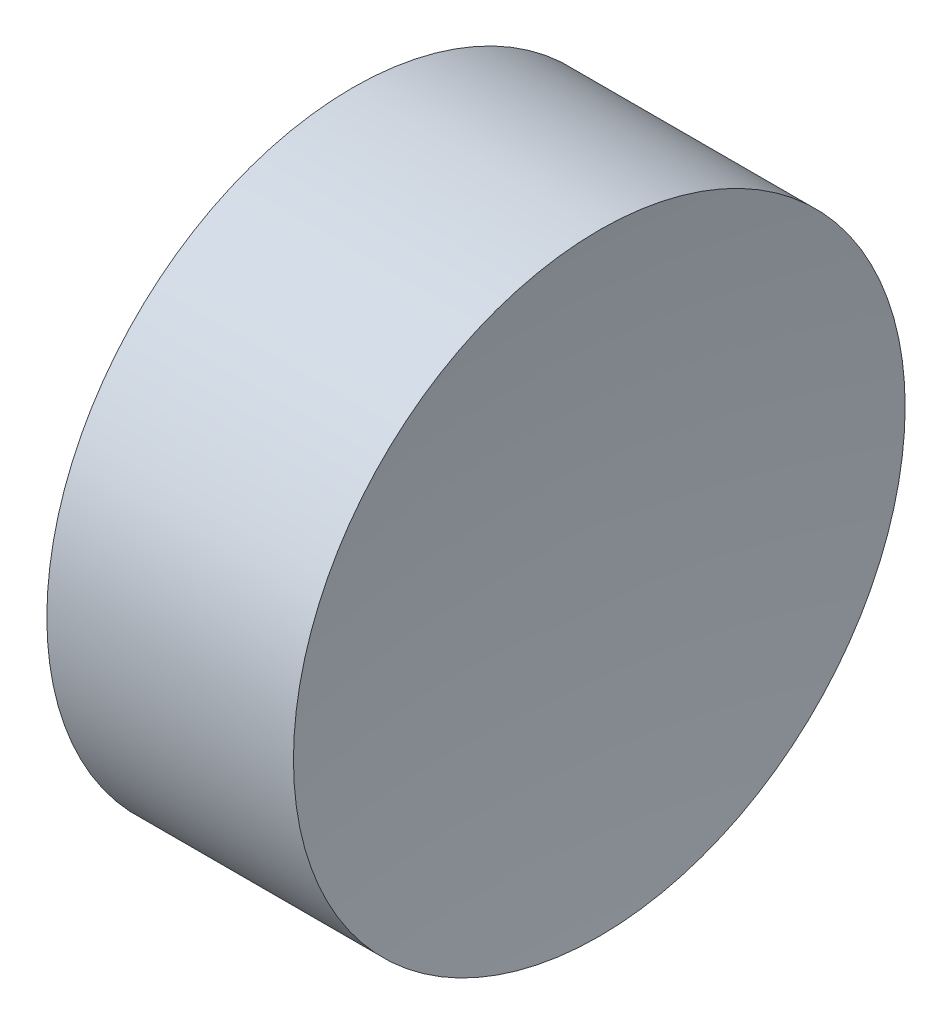
SolidWorks part; units mm, degrees
ref_plane "前视基准面" through (0, 0, 0) normal (0, 0, 1) x (1, 0, 0)
ref_plane "上视基准面" through (0, 0, 0) normal (0, 1, 0) x (1, 0, 0)
ref_plane "右视基准面" through (0, 0, 0) normal (1, 0, 0) x (0, 0, -1)
sketch "草图1" plane through (0, 0, 0) normal (0, 0, 1) x (1, 0, 0)
  line L0 (10.6125, 6.5223) -> (13.9161, 6.5223) construction
  line L1 (12.5141, 6.5223) -> (11.5141, 6.5223)
  line L3 (12.0141, 8.0223) -> (12.6159, 8.0223)
  line L4 (12.0141, 8.0223) -> (11.4064, 8.0223)
  arc A0 (12.6159, 8.0223) -> (12.5141, 6.5223) centre (23.014, 6.5636) ccw
  arc A1 (11.5141, 6.5223) -> (11.4064, 8.0223) centre (1.0141, 6.5223) ccw
revolve "旋转1" add sketch "草图1" angle 360 about L0
